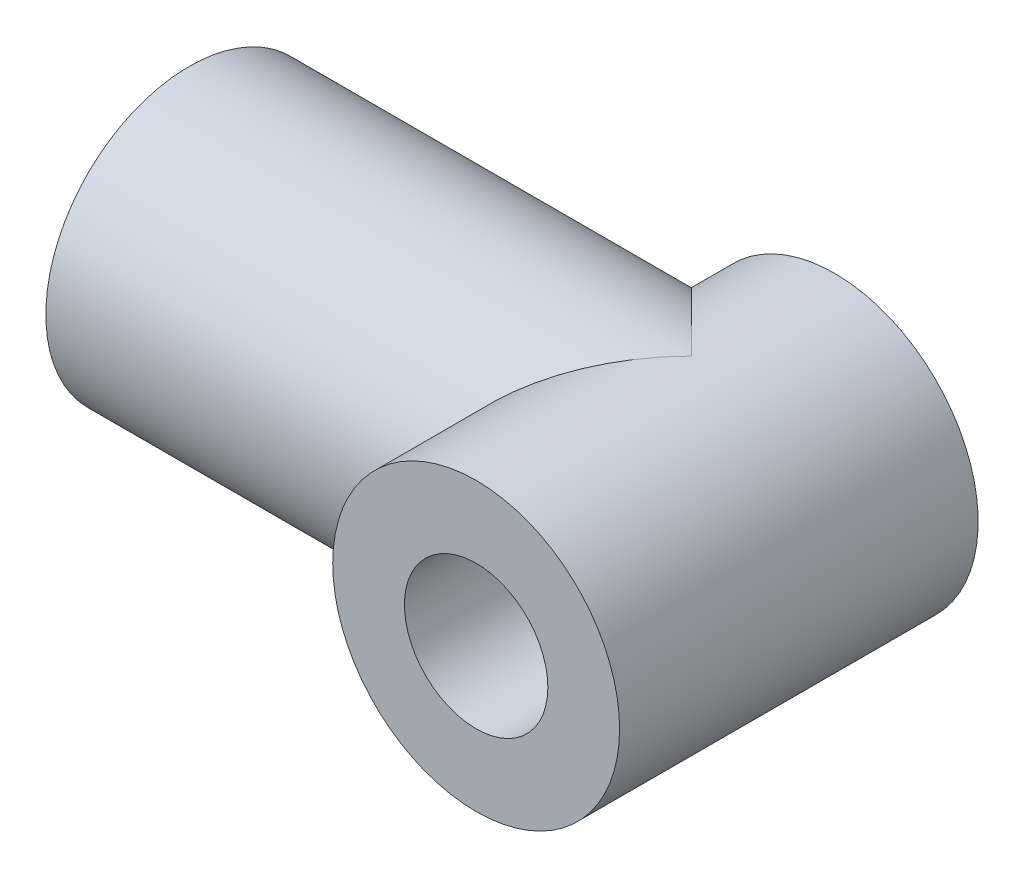
SolidWorks part; units mm, degrees
ref_plane "Front Plane" through (0, 0, 0) normal (0, 0, 1) x (1, 0, 0)
ref_plane "Top Plane" through (0, 0, 0) normal (0, 1, 0) x (1, 0, 0)
ref_plane "Right Plane" through (0, 0, 0) normal (1, 0, 0) x (0, 0, -1)
sketch "Sketch1" plane through (0, 0, 0) normal (0, 0, 1) x (1, 0, 0)
  circle A0 centre (0, 0) radius 3
  circle A1 centre (0, 0) radius 6
  dimension "D1" = 6
  dimension "D2" = 12
extrude "Boss-Extrude1" add sketch "Sketch1" along normal blind 15
sketch "Sketch2" plane through (0, 0, 0) normal (1, 0, 0) x (0, 0, -1)
  line L0 (0, -6) -> (0, 6) construction
  circle A0 centre (-6, 0) radius 3
  circle A1 centre (-6, 0) radius 6
  dimension "D1" = 6
  dimension "D2" = 12
  dimension "D3" = 6
extrude "Boss-Extrude2" add sketch "Sketch2" against normal blind 21
sketch "Sketch3" plane through (0, 0, 0) normal (0, 0, -1) x (-1, 0, 0)
  circle A0 centre (0, 0) radius 3
extrude "Cut-Extrude1" cut sketch "Sketch3" against normal through all
